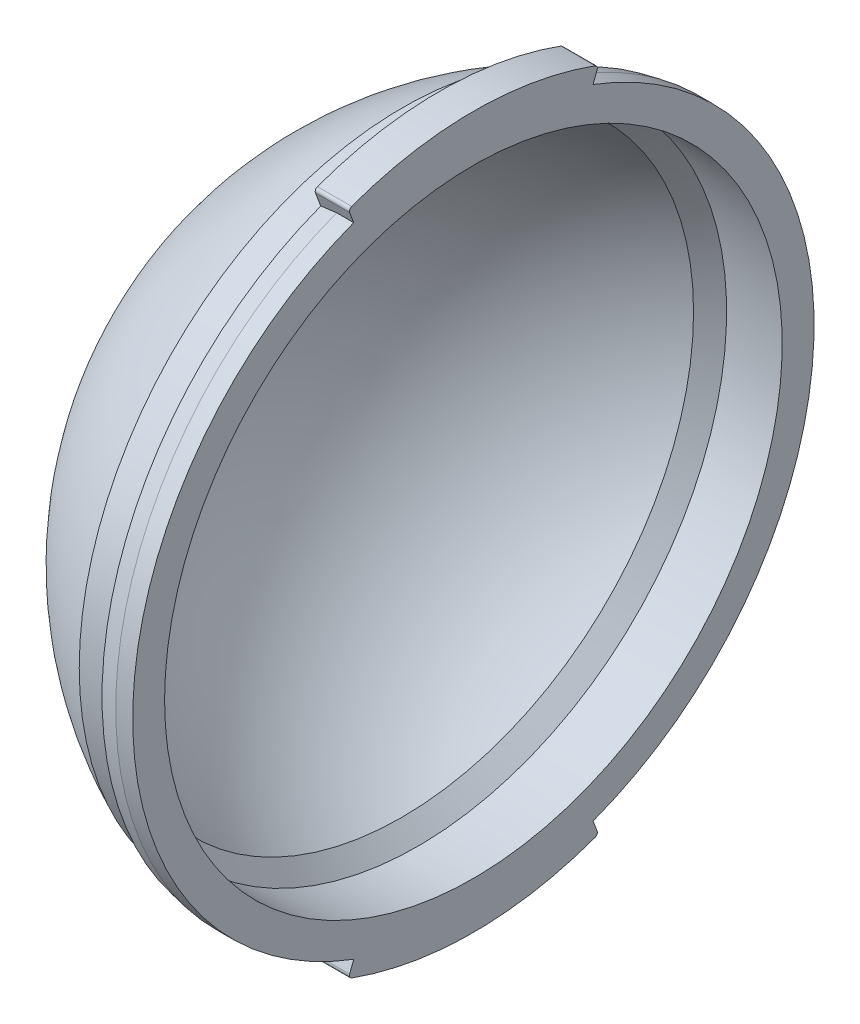
SolidWorks part; units mm, degrees
material "Acrylic (Medium-high impact)"
ref_plane "Front Plane" through (0, 0, 0) normal (0, 0, 1) x (1, 0, 0)
ref_plane "Top Plane" through (0, 0, 0) normal (0, 1, 0) x (1, 0, 0)
ref_plane "Right Plane" through (0, 0, 0) normal (1, 0, 0) x (0, 0, -1)
sketch "Sketch1" plane through (0, 0, 0) normal (0, 1, 0) x (1, 0, 0)
  line L0 (2.2245, 0) -> (86.4268, 0) construction
  line L1 (0, 46.0502) -> (-8.2931, 46.0502)
  line L2 (0, 46.0502) -> (0, 50.8)
  line L3 (0, 50.8) -> (-2.54, 50.8)
  line L4 (-2.54, 50.8) -> (-5.08, 50.3)
  line L5 (-5.08, 50.3) -> (-5.08, 48.26)
  line L6 (-5.08, 48.26) -> (-10.5174, 48.26)
  line L7 (-8.2931, 46.0502) -> (-10.6896, 43.5178)
  line L8 (-41.836, 0) -> (-37.62, 0)
  arc A0 (-10.5174, 48.26) -> (-41.836, 0) centre (11.0062, 0) ccw
  arc A1 (-10.6896, 43.5178) -> (-37.62, 0) centre (11.0062, 0) ccw
  dimension "D1" = 92.1004
  dimension "D2" = 101.6
  dimension "D3" = 96.52
  dimension "D4" = 5.08
  dimension "D5" = 2.54
  dimension "D6" = 0.5
  dimension "D7" = 4.216
  dimension "D8" = 8.2931
revolve "Revolve1" add sketch "Sketch1" angle 360 about L0
sketch "Sketch3" plane through (0, 0, 0) normal (1, 0, 0) x (0, 0, -1)
  line L0 (-16.8733, 44.9632) -> (-18.63, 49.6445)
  line L1 (18.63, 49.6445) -> (16.8733, 44.9632)
  line L2 (0, 5.2359) -> (0, 50005.2359) construction
  line L3 (-16.8733, 44.9632) -> (16.8733, 44.9632) construction
  circle A0 centre (0, 0) radius 53.025 construction
  arc A2 (-18.63, 49.6445) -> (18.63, 49.6445) centre (0, 0) cw
  arc A3 (-16.8733, 44.9632) -> (16.8733, 44.9632) centre (0, 0) cw
  dimension "D1" = 106.05
  dimension "D3" = 5
  dimension "D2" = 37.26
extrude "Boss-Extrude2" add sketch "Sketch3" against normal blind 5.1
fillet "Fillet1" radius 0.5 2 edges at (-2.55, 49.6445, -18.63) (-2.55, 49.6445, 18.63)
mirror "Mirror1" about plane through (0, 0, 0) normal (0, 1, 0) of "Fillet1", "Boss-Extrude2"
